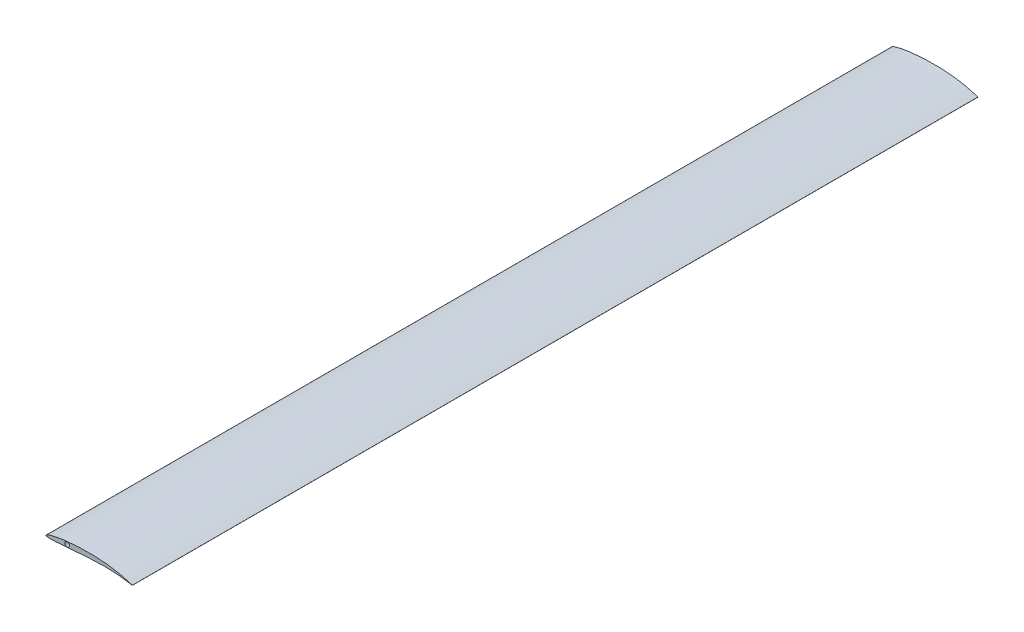
SolidWorks part; units mm, degrees
ref_plane "Front Plane" through (0, 0, 0) normal (0, 0, 1) x (1, 0, 0)
ref_plane "Top Plane" through (0, 0, 0) normal (0, 1, 0) x (1, 0, 0)
ref_plane "Right Plane" through (0, 0, 0) normal (1, 0, 0) x (0, 0, -1)
curve "Curve1"
  spline degree 3 poles (25.4, 0.016, 0) (25.3391, 0.0354, 0) (25.1691, 0.0896, 0) (24.8604, 0.1853, 0) (24.4521, 0.3079, 0) (23.9748, 0.4451, 0) (23.4435, 0.5905, 0) (22.8682, 0.7391, 0) (22.2564, 0.887, 0) (21.6142, 1.0313, 0) (20.9466, 1.1694, 0) (20.258, 1.299, 0) (19.5521, 1.4184, 0) (18.8325, 1.5262, 0) (18.1021, 1.6212, 0) (17.3637, 1.7024, 0) (16.6199, 1.7689, 0) (15.8731, 1.8208, 0) (15.1255, 1.8558, 0) (14.3793, 1.8809, 0) (13.6365, 1.8983, 0) (12.8989, 1.9074, 0) (12.1682, 1.9083, 0) (11.4461, 1.901, 0) (10.7342, 1.8857, 0) (10.0342, 1.8625, 0) (9.3474, 1.8315, 0) (8.6753, 1.7932, 0) (8.0194, 1.7478, 0) (7.3808, 1.6956, 0) (6.761, 1.637, 0) (6.1612, 1.5726, 0) (5.5826, 1.5027, 0) (5.0264, 1.428, 0) (4.4936, 1.3489, 0) (3.9856, 1.2661, 0) (3.5033, 1.1802, 0) (3.0477, 1.0919, 0) (2.6201, 1.0017, 0) (2.2213, 0.9105, 0) (1.8523, 0.8188, 0) (1.5142, 0.7273, 0) (1.2078, 0.6366, 0) (0.9341, 0.5475, 0) (0.694, 0.4605, 0) (0.4882, 0.3763, 0) (0.3176, 0.2954, 0) (0.1826, 0.2183, 0) (0.0836, 0.145, 0) (0.0195, 0.0755, 0) (-0.008, 0.0023, 0) (0.0173, -0.0678, 0) (0.0849, -0.1179, 0) (0.1842, -0.1582, 0) (0.3194, -0.1909, 0) (0.4898, -0.2162, 0) (0.6954, -0.2344, 0) (0.9354, -0.2455, 0) (1.209, -0.2497, 0) (1.5153, -0.2472, 0) (1.8533, -0.2383, 0) (2.2222, -0.2234, 0) (2.621, -0.2028, 0) (3.0486, -0.1768, 0) (3.504, -0.1458, 0) (3.9863, -0.1104, 0) (4.4943, -0.0708, 0) (5.0269, -0.0277, 0) (5.5831, 0.0186, 0) (6.1617, 0.0673, 0) (6.7614, 0.1181, 0) (7.3812, 0.1704, 0) (8.0196, 0.2236, 0) (8.6755, 0.2771, 0) (9.3475, 0.3304, 0) (10.0343, 0.3829, 0) (10.7343, 0.4341, 0) (11.446, 0.4835, 0) (12.1681, 0.5305, 0) (12.8988, 0.5746, 0) (13.6364, 0.6156, 0) (14.3791, 0.6529, 0) (15.1252, 0.6867, 0) (15.8725, 0.7144, 0) (16.6192, 0.7287, 0) (17.363, 0.7312, 0) (18.1013, 0.7217, 0) (18.8317, 0.7006, 0) (19.5514, 0.6682, 0) (20.2572, 0.6255, 0) (20.9458, 0.5732, 0) (21.6134, 0.5125, 0) (22.2557, 0.4449, 0) (22.8675, 0.3721, 0) (23.4429, 0.2962, 0) (23.9743, 0.2197, 0) (24.4517, 0.1457, 0) (24.8601, 0.0785, 0) (25.1689, 0.0253, 0) (25.3391, -0.0051, 0) (25.4, -0.016, 0) knots 0 0 0 0 0.003729 0.010403 0.018841 0.028586 0.039358 0.050957 0.063231 0.076057 0.089334 0.102977 0.11691 0.131071 0.145402 0.159854 0.17438 0.18894 0.203496 0.218017 0.232469 0.246817 0.261029 0.275074 0.288921 0.302543 0.315913 0.329004 0.341791 0.35425 0.366358 0.37809 0.389424 0.400339 0.410813 0.420824 0.430352 0.439376 0.447877 0.455834 0.463229 0.470043 0.476257 0.481856 0.486823 0.491146 0.494814 0.497827 0.500195 0.50197 0.5033 0.504509 0.506013 0.508063 0.510747 0.514093 0.518105 0.522777 0.528099 0.534057 0.540634 0.547815 0.555582 0.563914 0.572793 0.582198 0.592109 0.602502 0.613357 0.624649 0.636356 0.648452 0.660912 0.673711 0.686822 0.700217 0.713868 0.727745 0.741819 0.756057 0.770426 0.784892 0.799419 0.813968 0.828496 0.842964 0.85733 0.871548 0.885567 0.89933 0.912776 0.925832 0.938415 0.950429 0.961757 0.972255 0.981732 0.989922 0.99639 1 1 1 1
sketch "Sketch3" plane through (0, 0, 0) normal (0, 0, 1) x (1, 0, 0)
  line L0 (25.4, 0.016) -> (25.4, -0.016)
  line L1 (0, 0) -> (25.4, 0) construction
  spline S0 degree 3 poles (669.244, 1893.2813) (49.9556, -17.1731) (38.8562, -4.1548) (24.8604, 0.1853) (24.4521, 0.3079) (23.7837, 0.5001) (22.615, 0.8106) (21.3697, 1.0897) (20.0193, 1.3439) (19.0695, 1.4954) (18.1021, 1.6212) (17.3637, 1.7024) (16.6199, 1.7689) (15.8731, 1.8208) (15.1255, 1.8558) (14.3793, 1.8809) (13.6365, 1.8983) (12.658, 1.9103) (11.6898, 1.9063) (10.505, 1.8807) (9.5807, 1.8449) (8.6753, 1.7932) (8.0194, 1.7478) (7.3808, 1.6956) (6.761, 1.637) (6.1612, 1.5726) (5.5826, 1.5027) (5.0264, 1.428) (4.4936, 1.3489) (3.9856, 1.2661) (3.5033, 1.1802) (3.0477, 1.0919) (2.6201, 1.0017) (2.2213, 0.9105) (1.8523, 0.8188) (1.5142, 0.7273) (1.2078, 0.6366) (0.9341, 0.5475) (0.694, 0.4605) (0.4882, 0.3763) (0.3176, 0.2954) (0.1826, 0.2183) (0.0836, 0.145) (0.0195, 0.0755) (-0.008, 0.0023) (0.0173, -0.0678) (0.0849, -0.1179) (0.1842, -0.1582) (0.3194, -0.1909) (0.4898, -0.2162) (0.6954, -0.2344) (0.9354, -0.2455) (1.209, -0.2497) (1.5153, -0.2472) (1.8533, -0.2383) (2.2222, -0.2234) (2.621, -0.2028) (3.0486, -0.1768) (3.504, -0.1458) (3.9863, -0.1104) (4.4943, -0.0708) (5.0269, -0.0277) (5.5831, 0.0186) (6.1617, 0.0673) (6.7614, 0.1181) (7.3812, 0.1704) (8.0196, 0.2236) (8.6755, 0.2771) (9.5809, 0.3489) (10.7458, 0.4363) (11.9305, 0.5161) (12.8988, 0.5746) (13.6364, 0.6156) (14.3791, 0.6529) (15.1252, 0.6867) (15.8725, 0.7144) (16.6192, 0.7287) (17.363, 0.7312) (18.1013, 0.7217) (19.0677, 0.6937) (20.2411, 0.6319) (21.5894, 0.5195) (22.6536, 0.4003) (23.4429, 0.2962) (23.9743, 0.2197) (24.4517, 0.1457) (24.8601, 0.0785) (40.0053, -2.5297) (53.5468, -13.3976) (418.1188, 1960.8142) knots -0.835522 -0.835522 -0.835522 -0.835522 0.003729 0.010403 0.018841 0.028586 0.050957 0.089334 0.102977 0.131071 0.145402 0.159854 0.17438 0.18894 0.203496 0.218017 0.232469 0.246817 0.275074 0.288921 0.315913 0.329004 0.341791 0.35425 0.366358 0.37809 0.389424 0.400339 0.410813 0.420824 0.430352 0.439376 0.447877 0.455834 0.463229 0.470043 0.476257 0.481856 0.486823 0.491146 0.494814 0.497827 0.500195 0.50197 0.5033 0.504509 0.506013 0.508063 0.510747 0.514093 0.518105 0.522777 0.528099 0.534057 0.540634 0.547815 0.555582 0.563914 0.572793 0.582198 0.592109 0.602502 0.613357 0.624649 0.636356 0.648452 0.660912 0.673711 0.686822 0.713868 0.741819 0.756057 0.770426 0.784892 0.799419 0.813968 0.828496 0.842964 0.85733 0.871548 0.89933 0.925832 0.950429 0.961757 0.972255 0.981732 0.989922 0.99639 1.877782 1.877782 1.877782 1.877782 only from (25.4, 0.016) to (25.4, -0.016) construction
  spline S1 degree 3 poles (25.4, 0.016) (25.3391, 0.0354) (25.1691, 0.0896) (24.8604, 0.1853) (24.4521, 0.3079) (23.7837, 0.5001) (22.615, 0.8106) (21.3697, 1.0897) (20.0193, 1.3439) (19.0695, 1.4954) (18.1021, 1.6212) (17.3637, 1.7024) (16.6199, 1.7689) (15.8731, 1.8208) (15.1255, 1.8558) (14.3793, 1.8809) (13.6365, 1.8983) (12.658, 1.9103) (11.6898, 1.9063) (10.505, 1.8807) (9.5807, 1.8449) (8.6753, 1.7932) (8.0194, 1.7478) (7.3808, 1.6956) (6.761, 1.637) (6.1612, 1.5726) (5.5826, 1.5027) (5.0264, 1.428) (4.4936, 1.3489) (3.9856, 1.2661) (3.5033, 1.1802) (3.0477, 1.0919) (2.6201, 1.0017) (2.2213, 0.9105) (1.8523, 0.8188) (1.5142, 0.7273) (1.2078, 0.6366) (0.9341, 0.5475) (0.694, 0.4605) (0.4882, 0.3763) (0.3176, 0.2954) (0.1826, 0.2183) (0.0836, 0.145) (0.0195, 0.0755) (-0.008, 0.0023) (0.0173, -0.0678) (0.0849, -0.1179) (0.1842, -0.1582) (0.3194, -0.1909) (0.4898, -0.2162) (0.6954, -0.2344) (0.9354, -0.2455) (1.209, -0.2497) (1.5153, -0.2472) (1.8533, -0.2383) (2.2222, -0.2234) (2.621, -0.2028) (3.0486, -0.1768) (3.504, -0.1458) (3.9863, -0.1104) (4.4943, -0.0708) (5.0269, -0.0277) (5.5831, 0.0186) (6.1617, 0.0673) (6.7614, 0.1181) (7.3812, 0.1704) (8.0196, 0.2236) (8.6755, 0.2771) (9.5809, 0.3489) (10.7458, 0.4363) (11.9305, 0.5161) (12.8988, 0.5746) (13.6364, 0.6156) (14.3791, 0.6529) (15.1252, 0.6867) (15.8725, 0.7144) (16.6192, 0.7287) (17.363, 0.7312) (18.1013, 0.7217) (19.0677, 0.6937) (20.2411, 0.6319) (21.5894, 0.5195) (22.6536, 0.4003) (23.4429, 0.2962) (23.9743, 0.2197) (24.4517, 0.1457) (24.8601, 0.0785) (25.1689, 0.0253) (25.3391, -0.0051) (25.4, -0.016) knots 0 0 0 0 0.003729 0.010403 0.018841 0.028586 0.050957 0.089334 0.102977 0.131071 0.145402 0.159854 0.17438 0.18894 0.203496 0.218017 0.232469 0.246817 0.275074 0.288921 0.315913 0.329004 0.341791 0.35425 0.366358 0.37809 0.389424 0.400339 0.410813 0.420824 0.430352 0.439376 0.447877 0.455834 0.463229 0.470043 0.476257 0.481856 0.486823 0.491146 0.494814 0.497827 0.500195 0.50197 0.5033 0.504509 0.506013 0.508063 0.510747 0.514093 0.518105 0.522777 0.528099 0.534057 0.540634 0.547815 0.555582 0.563914 0.572793 0.582198 0.592109 0.602502 0.613357 0.624649 0.636356 0.648452 0.660912 0.673711 0.686822 0.713868 0.741819 0.756057 0.770426 0.784892 0.799419 0.813968 0.828496 0.842964 0.85733 0.871548 0.89933 0.925832 0.950429 0.961757 0.972255 0.981732 0.989922 0.99639 1 1 1 1
sketch "Sketch4" plane through (0, 0, 0) normal (0, 0, 1) x (1, 0, 0)
  line L0 (155.702, 0.0981) -> (155.702, -0.0981)
  line L1 (38.0589, 0.4374) -> (38.0589, 9.6648) construction
  line L2 (69.3921, 2.9083) -> (69.3921, 11.6318) construction
  line L3 (110.1735, 4.4273) -> (110.1735, 10.0164) construction
  circle A1 centre (38.0589, 5.0511) radius 4.1906
  spline S0 degree 3 poles (0, 0) (22.9753, 3.8799) (74.9406, 9.1602) (127.4828, 7.8166) (155.702, 0) knots 0 0 0 0 0.445511 1 1 1 1 construction
  spline S1 degree 3 poles (155.702, 0.0981) (155.3285, 0.2171) (154.2864, 0.5491) (152.3944, 1.1358) (149.8914, 1.8872) (145.7938, 3.0657) (138.6302, 4.969) (130.996, 6.68) (122.7181, 8.2382) (116.8959, 9.1669) (110.9657, 9.9379) (106.4394, 10.4355) (101.88, 10.8435) (97.3024, 11.1613) (92.7193, 11.3762) (88.1454, 11.5296) (83.592, 11.6365) (77.5937, 11.7103) (71.6583, 11.6853) (64.3955, 11.529) (58.7295, 11.309) (53.1798, 10.9924) (49.1588, 10.7138) (45.2446, 10.3938) (41.4452, 10.0349) (37.7683, 9.6398) (34.2213, 9.2115) (30.8115, 8.7534) (27.546, 8.2687) (24.4316, 7.7613) (21.4749, 7.2348) (18.6826, 6.6933) (16.061, 6.1407) (13.6164, 5.5812) (11.3547, 5.019) (9.2819, 4.458) (7.4038, 3.9025) (5.726, 3.3562) (4.254, 2.8231) (2.9926, 2.3069) (1.9468, 1.8107) (1.1195, 1.3385) (0.5124, 0.8888) (0.1196, 0.463) (-0.0493, 0.0142) (0.1059, -0.4154) (0.5205, -0.7229) (1.1292, -0.97) (1.9577, -1.1701) (3.0025, -1.3256) (4.263, -1.4369) (5.7342, -1.5048) (7.4113, -1.5305) (9.2888, -1.5153) (11.361, -1.4611) (13.6222, -1.3697) (16.0665, -1.2431) (18.6877, -1.0837) (21.4796, -0.894) (24.4359, -0.6765) (27.5499, -0.434) (30.8151, -0.1696) (34.2245, 0.1138) (37.7711, 0.4128) (41.4476, 0.7243) (45.2466, 1.0447) (49.1604, 1.3707) (53.181, 1.6988) (58.7311, 2.1389) (65.8715, 2.6744) (73.134, 3.1636) (79.0694, 3.5225) (83.5909, 3.7738) (88.1441, 4.0022) (92.7172, 4.2096) (97.2985, 4.3792) (101.8759, 4.4666) (106.435, 4.4823) (110.9611, 4.424) (116.8849, 4.2525) (124.0777, 3.8736) (132.3432, 3.1848) (138.8663, 2.4541) (143.7052, 1.8156) (146.9626, 1.3465) (149.8889, 0.8932) (152.3926, 0.481) (154.2854, 0.155) (155.3284, -0.0313) (155.702, -0.0981) knots 0 0 0 0 0.003729 0.010403 0.018841 0.028586 0.050957 0.089334 0.102977 0.131071 0.145402 0.159854 0.17438 0.18894 0.203496 0.218017 0.232469 0.246817 0.275074 0.288921 0.315913 0.329004 0.341791 0.35425 0.366358 0.37809 0.389424 0.400339 0.410813 0.420824 0.430352 0.439376 0.447877 0.455834 0.463229 0.470043 0.476257 0.481856 0.486823 0.491146 0.494814 0.497827 0.500195 0.50197 0.5033 0.504509 0.506013 0.508063 0.510747 0.514093 0.518105 0.522777 0.528099 0.534057 0.540634 0.547815 0.555582 0.563914 0.572793 0.582198 0.592109 0.602502 0.613357 0.624649 0.636356 0.648452 0.660912 0.673711 0.686822 0.713868 0.741819 0.756057 0.770426 0.784892 0.799419 0.813968 0.828496 0.842964 0.85733 0.871548 0.89933 0.925832 0.950429 0.961757 0.972255 0.981732 0.989922 0.99639 1 1 1 1
  point P8 (38.0589, 5.0511)
  point P9 (69.3921, 7.27)
  point P10 (110.1735, 7.2219)
  dimension "D1" = 8.3811
extrude "Boss-Extrude1" add sketch "Sketch4" along normal blind 1524
